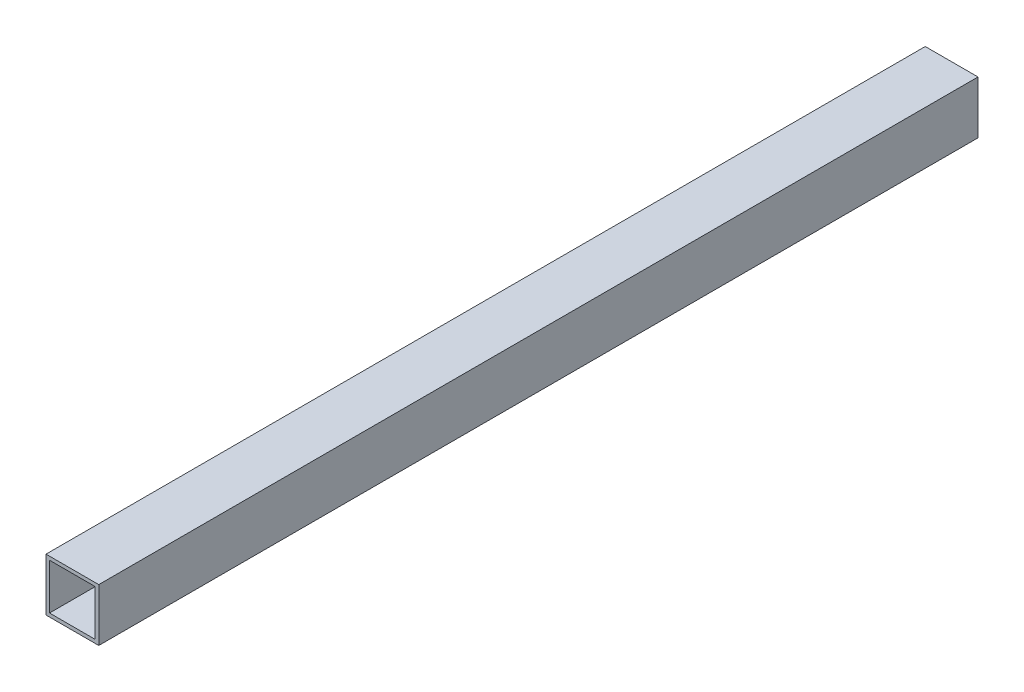
SolidWorks part; units mm, degrees
material "1.0037 (S235JR)"
ref_plane "Front Plane" through (0, 0, 0) normal (0, 0, 1) x (1, 0, 0)
ref_plane "Top Plane" through (0, 0, 0) normal (0, 1, 0) x (1, 0, 0)
ref_plane "Right Plane" through (0, 0, 0) normal (1, 0, 0) x (0, 0, -1)
curve "Curve1"
  spline degree 1 poles (0, 0, 0) (0, 0, 1000) knots 0 0 1 1
sketch "Sketch1" plane through (0, 0, 0) normal (0, 0, 1) x (1, 0, 0)
  line L0 (0, 35.3535) -> (0, -33.8384) construction
  line L1 (-30, 30) -> (30, 30)
  line L2 (-30, 30) -> (-30, -30)
  line L3 (-30, -30) -> (30, -30)
  line L4 (30, 30) -> (30, -30)
  line L5 (-26, 26) -> (26, 26)
  line L6 (-26, 26) -> (-26, -26)
  line L7 (-26, -26) -> (26, -26)
  line L8 (26, 26) -> (26, -26)
  line L9 (-39.3939, 0) -> (41.5152, 0) construction
  dimension "D1" = 60
  dimension "D2" = 52
sweep "Sweep1" add profiles "Sketch1" path "Curve1"
